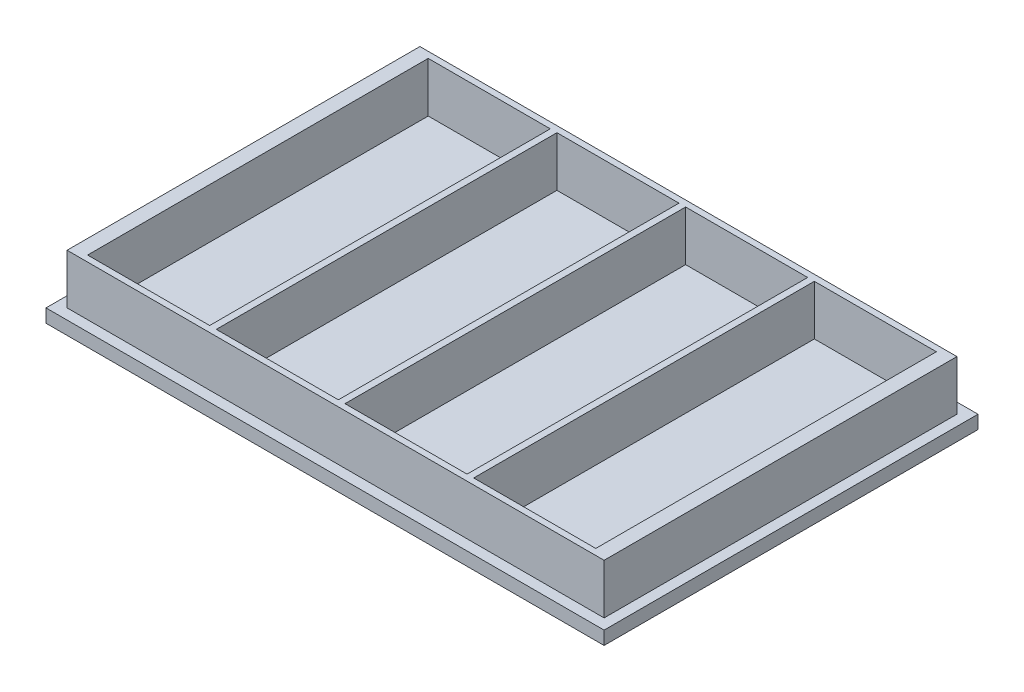
SolidWorks part; units mm, degrees
material "ABS PC"
ref_plane "Front Plane" through (0, 0, 0) normal (0, 0, 1) x (1, 0, 0)
ref_plane "Top Plane" through (0, 0, 0) normal (0, 1, 0) x (1, 0, 0)
ref_plane "Right Plane" through (0, 0, 0) normal (1, 0, 0) x (0, 0, -1)
sketch "Sketch1" plane through (0, 0, 0) normal (0, 1, 0) x (1, 0, 0)
  line L1 (0, 0) -> (127.762, 0)
  line L2 (0, 0) -> (0, -85.598)
  line L3 (0, -85.598) -> (127.762, -85.598)
  line L4 (127.762, 0) -> (127.762, -85.598)
  line L5 (2.413, -2.413) -> (125.349, -2.413)
  line L6 (2.413, -2.413) -> (2.413, -83.185)
  line L7 (2.413, -83.185) -> (125.349, -83.185)
  line L8 (125.349, -2.413) -> (125.349, -83.185)
  dimension "D1" = 127.762
  dimension "D2" = 85.598
  dimension "D3" = 2.413
  dimension "D4" = 2.413
  dimension "D5" = 2.413
  dimension "D6" = 2.413
extrude "Boss-Extrude1" add sketch "Sketch1" along normal blind 3.048
sketch "Sketch2" plane through (0, 3.048, 0) normal (0, 1, 0) x (1, 0, 0)
  line L1 (2.413, -2.413) -> (125.349, -2.413)
  line L2 (2.413, -2.413) -> (2.413, -83.185)
  line L3 (2.413, -83.185) -> (125.349, -83.185)
  line L4 (125.349, -2.413) -> (125.349, -83.185)
extrude "Boss-Extrude2" add sketch "Sketch2" against normal blind 2.413
sketch "Sketch3" plane through (0, 3.048, 0) normal (0, 1, 0) x (1, 0, 0)
  line L1 (2.413, -2.413) -> (125.349, -2.413)
  line L2 (2.413, -2.413) -> (2.413, -83.185)
  line L3 (2.413, -83.185) -> (125.349, -83.185)
  line L4 (125.349, -2.413) -> (125.349, -83.185)
  line L5 (5.715, -3.81) -> (122.047, -3.81)
  line L6 (5.715, -3.81) -> (5.715, -81.788)
  line L7 (5.715, -81.788) -> (122.047, -81.788)
  line L8 (122.047, -3.81) -> (122.047, -81.788)
  line L9 (33.655, -3.81) -> (35.179, -3.81)
  line L10 (33.655, -3.81) -> (33.655, -81.788)
  line L11 (33.655, -81.788) -> (35.179, -81.788)
  line L12 (35.179, -3.81) -> (35.179, -81.788)
  line L13 (63.119, -81.788) -> (64.643, -81.788)
  line L14 (63.119, -81.788) -> (63.119, -3.81)
  line L15 (63.119, -3.81) -> (64.643, -3.81)
  line L16 (64.643, -81.788) -> (64.643, -3.81)
  line L17 (92.583, -81.788) -> (94.107, -81.788)
  line L18 (92.583, -81.788) -> (92.583, -3.81)
  line L19 (92.583, -3.81) -> (94.107, -3.81)
  line L20 (94.107, -81.788) -> (94.107, -3.81)
  dimension "D1" = 77.978
  dimension "D2" = 3.302
  dimension "D3" = 27.94
  dimension "D4" = 1.397
  dimension "D5" = 1.524
  dimension "D6" = 1.524
  dimension "D7" = 1.524
  dimension "D8" = 27.94
  dimension "D9" = 27.94
  dimension "D10" = 27.94
extrude "Boss-Extrude3" add sketch "Sketch3" along normal blind 11.43 contours L4 L1 L2 L3 L5 L8 L7 L6 | L10 L11 L12 L9 | L14 L15 L16 L13 | L18 L19 L20 L17
